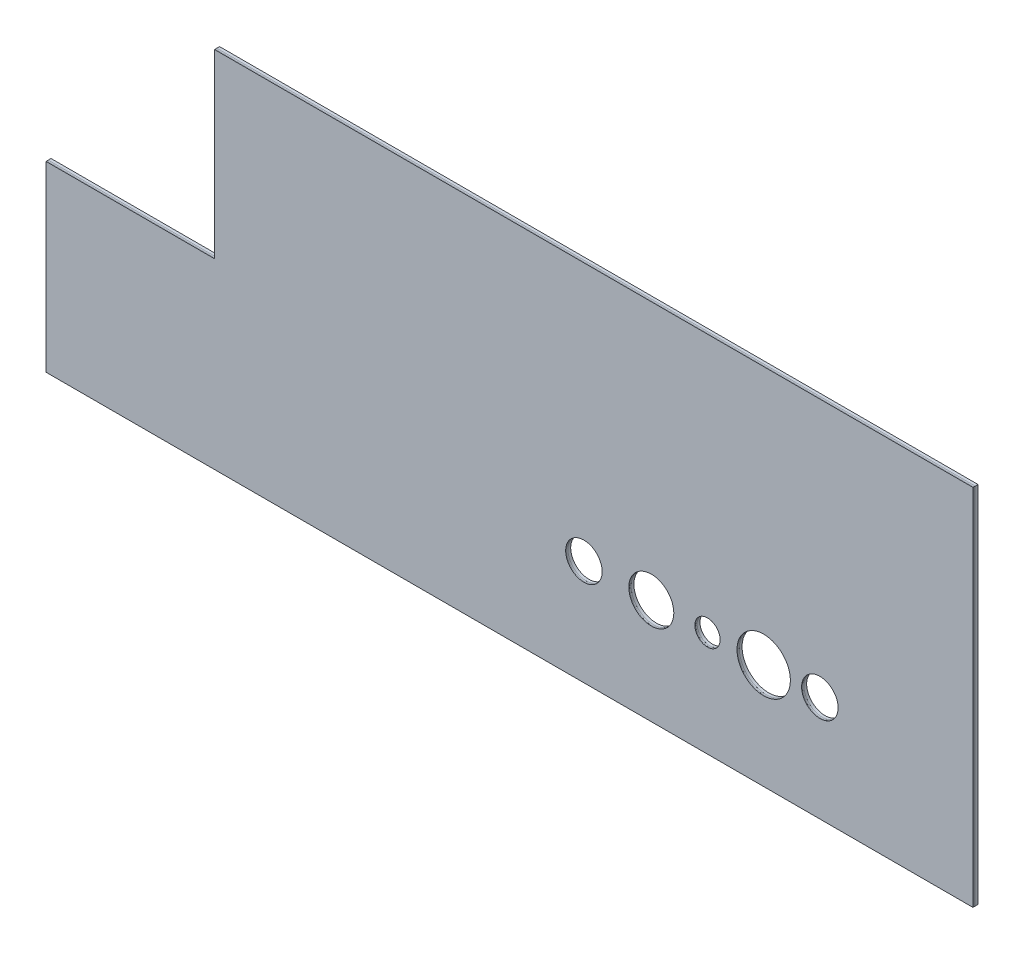
SolidWorks part; units mm, degrees
ref_plane "Płaszczyzna przednia" through (0, 0, 0) normal (0, 0, 1) x (1, 0, 0)
ref_plane "Płaszczyzna górna" through (0, 0, 0) normal (0, 1, 0) x (1, 0, 0)
ref_plane "Płaszczyzna prawa" through (0, 0, 0) normal (1, 0, 0) x (0, 0, -1)
sketch "Szkic1" plane through (0, 0, 0) normal (0, 0, 1) x (1, 0, 0)
  line L0 (0, 0) -> (0, 129.5)
  line L1 (0, 0) -> (-330, 0)
  line L5 (0, 129.5) -> (-270, 129.5)
  line L6 (-270, 129.5) -> (-270, 65)
  line L7 (-270, 65) -> (-330, 65)
  line L8 (-330, 65) -> (-330, 0)
  dimension "D1" = 330
  dimension "D2" = 60
  dimension "D3" = 129.5
  dimension "D4" = 65
extrude "Dodanie-wyciągnięcie1" add sketch "Szkic1" along normal blind 1
sketch "Szkic2" plane through (0, 0, 1) normal (0, 0, 1) x (1, 0, 0)
  line L10 (0, 0) -> (-330, 0)
  line L11 (-330, 0) -> (-330, 65)
  line L12 (-330, 65) -> (-270, 65)
  line L13 (-270, 65) -> (-270, 129.5)
  line L14 (-270, 129.5) -> (0, 129.5)
  line L15 (0, 129.5) -> (0, 0)
extrude "Dodanie-wyciągnięcie2" add sketch "Szkic2" along normal blind 0.5 separate body
sketch "Szkic3" plane through (0, 0, 1.5) normal (0, 0, 1) x (1, 0, 0)
  line L0 (0, 0) -> (0, 129.5)
  line L5 (0, 129.5) -> (-270, 129.5)
  line L6 (-270, 129.5) -> (-270, 65)
  line L7 (-270, 65) -> (-330, 65)
  line L8 (-330, 65) -> (-330, 0)
  line L9 (-330, 0) -> (0, 0)
extrude "Dodanie-wyciągnięcie3" add sketch "Szkic3" along normal blind 0.3 separate body
sketch "Szkic4" plane through (0, 0, 1.8) normal (0, 0, 1) x (1, 0, 0)
  line L0 (0, 37.5) -> (-330, 37.5) construction
  line L1 (0, 0) -> (0, 129.5) construction
  line L2 (-330, 65) -> (-330, 0) construction
  line L3 (-330, 0) -> (0, 0) construction
  circle A0 centre (-74.5, 37.5) radius 9.5
  circle A1 centre (-94.5, 37.5) radius 4.5
  circle A2 centre (-114.5, 37.5) radius 8
  circle A3 centre (-138.5, 37.5) radius 6.5
  circle A4 centre (-54.5, 37.5) radius 6.5
  point P18 (-92.8623, 37.5)
  dimension "D1" = 19
  dimension "D3" = 9
  dimension "D4" = 16
  dimension "D5" = 13
  dimension "D6" = 13
  dimension "D8" = 20
  dimension "D2" = 37.5
  dimension "D7" = 74.5
  dimension "D9" = 20
  dimension "D10" = 24
  dimension "D11" = 20
extrude "Wytnij-wyciągnięcie1" cut sketch "Szkic4" against normal through all
